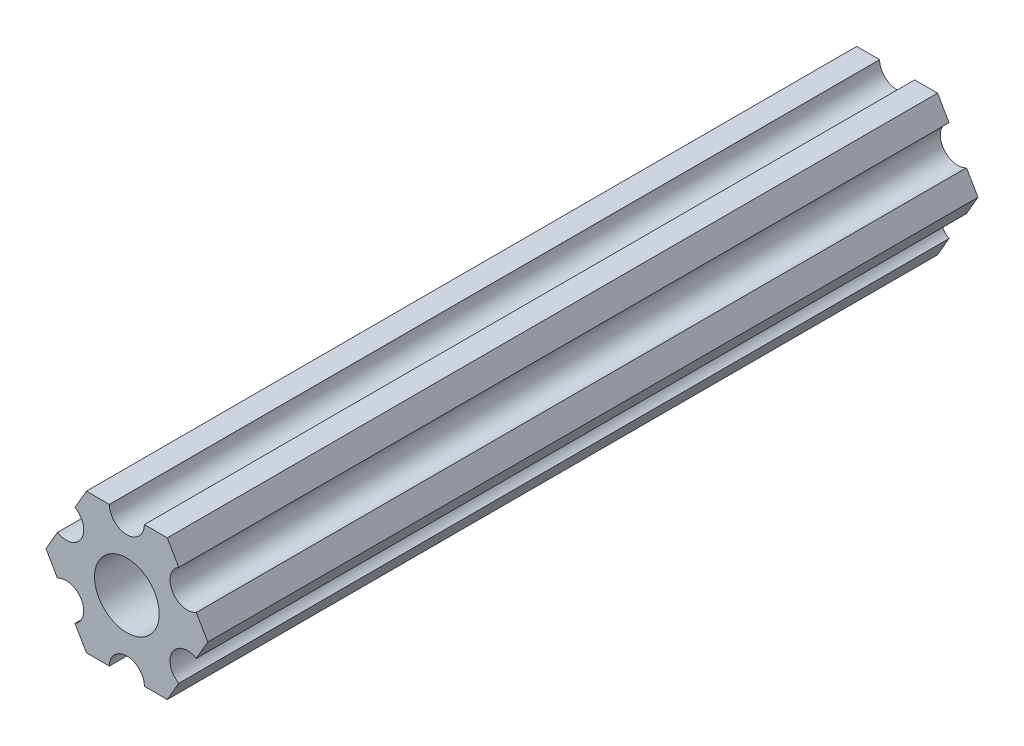
SolidWorks part; units mm, degrees
ref_plane "Front Plane" through (0, 0, 0) normal (0, 0, 1) x (1, 0, 0)
ref_plane "Top Plane" through (0, 0, 0) normal (0, 1, 0) x (1, 0, 0)
ref_plane "Right Plane" through (0, 0, 0) normal (1, 0, 0) x (0, 0, -1)
ref_plane "Plane1" through (0, 0, 0) normal (0, 0, -1) x (-1, 0, 0)
sketch "Sketch1" plane through (0, 0, 0) normal (0, 0, -1) x (-1, 0, 0)
  line L0 (-4.7055, -4.5498) -> (-3.6662, -6.35)
  line L1 (-3.6662, -6.35) -> (-1.5875, -6.35)
  line L2 (1.5875, -6.35) -> (3.6662, -6.35)
  line L3 (3.6662, -6.35) -> (4.7055, -4.5498)
  line L4 (6.293, -1.8002) -> (7.3323, 0)
  line L5 (7.3323, 0) -> (6.293, 1.8002)
  line L6 (4.7055, 4.5498) -> (3.6662, 6.35)
  line L7 (3.6662, 6.35) -> (1.5875, 6.35)
  line L8 (-1.5875, 6.35) -> (-3.6662, 6.35)
  line L9 (-3.6662, 6.35) -> (-4.7055, 4.5498)
  line L10 (-6.293, 1.8002) -> (-7.3323, 0)
  line L11 (-7.3323, 0) -> (-6.293, -1.8002)
  circle A0 centre (0, 0) radius 2.9337
  arc A1 (-6.293, -1.8002) -> (-4.7055, -4.5498) centre (-5.4993, -3.175) cw
  arc A2 (-1.5875, -6.35) -> (1.5875, -6.35) centre (0, -6.35) cw
  arc A3 (4.7055, -4.5498) -> (6.293, -1.8002) centre (5.4993, -3.175) cw
  arc A4 (6.293, 1.8002) -> (4.7055, 4.5498) centre (5.4993, 3.175) cw
  arc A5 (1.5875, 6.35) -> (-1.5875, 6.35) centre (0, 6.35) cw
  arc A6 (-4.7055, 4.5498) -> (-6.293, 1.8002) centre (-5.4993, 3.175) cw
extrude "Boss-Extrude1" add sketch "Sketch1" along normal blind 69.85
